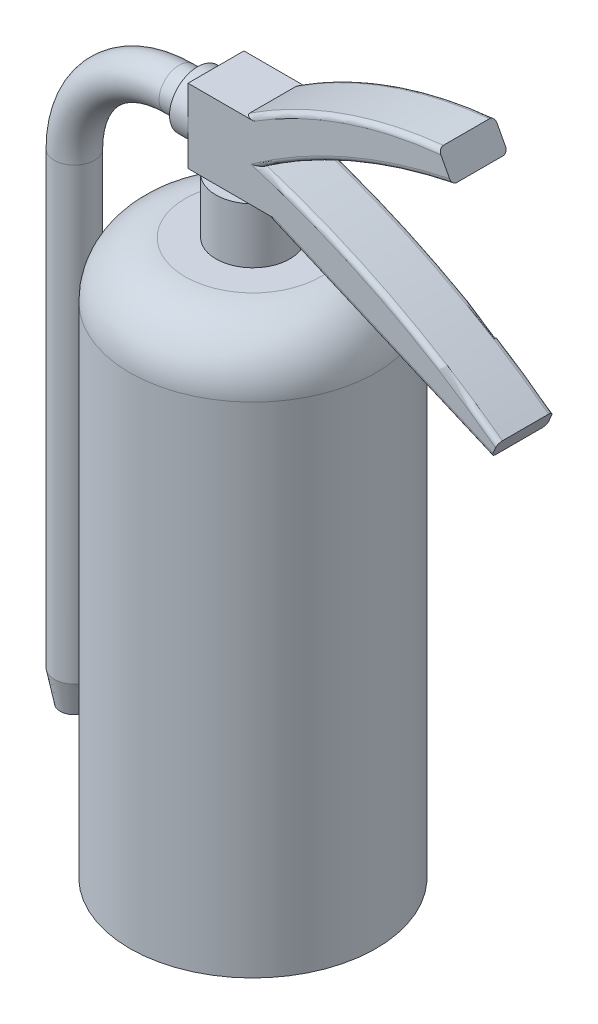
SolidWorks part; units mm, degrees
ref_plane "Alzado" through (0, 0, 0) normal (0, 0, 1) x (1, 0, 0)
ref_plane "Planta" through (0, 0, 0) normal (0, 1, 0) x (1, 0, 0)
ref_plane "Vista lateral" through (0, 0, 0) normal (1, 0, 0) x (0, 0, -1)
sketch "Croquis1" plane through (0, 0, 0) normal (0, 1, 0) x (1, 0, 0)
  circle A0 centre (0, 0) radius 200
  dimension "D1" = 400
extrude "Saliente-Extruir1" add sketch "Croquis1" along normal blind 900
fillet "Redondeo1" radius 90 1 edges at (0, 900, 200)
sketch "Croquis2" plane through (0, 900, 0) normal (0, 1, 0) x (1, 0, 0)
  circle A0 centre (0, 0) radius 60
  dimension "D1" = 120
extrude "Saliente-Extruir2" add sketch "Croquis2" along normal blind 90
sketch "Croquis3" plane through (0, 990, 0) normal (0, 1, 0) x (1, 0, 0)
  line L1 (60, -45.4181) -> (-60, -45.4181)
  line L2 (60, -45.4181) -> (60, 45.4181)
  line L3 (60, 45.4181) -> (-60, 45.4181)
  line L4 (-60, -45.4181) -> (-60, 45.4181)
  line L5 (60, -45.4181) -> (-60, 45.4181) construction
  line L6 (60, 45.4181) -> (-60, -45.4181) construction
  point P0 (0, 0)
extrude "Saliente-Extruir3" add sketch "Croquis3" along normal blind 60
sketch "Croquis4" plane through (0, 0, 45.4181) normal (0, 0, 1) x (1, 0, 0)
  line L0 (60, 990) -> (432.3041, 829.8986)
  line L1 (442.8785, 854.4887) -> (432.3041, 829.8986)
  line L2 (60, 1050) -> (60, 990)
  arc A0 (60, 1050) -> (442.8785, 854.4887) centre (-321.8825, -170.5176) cw
extrude "Saliente-Extruir4" add sketch "Croquis4" against normal up to surface (90.8363 mm away) up to face at (0, 1010, -45.4181)
sketch "Croquis5" plane through (0, 1050, 0) normal (0, 1, 0) x (1, 0, 0)
  line L1 (-60, 45.4181) -> (60, 45.4181)
  line L2 (-60, 45.4181) -> (-60, -45.4181)
  line L3 (-60, -45.4181) -> (60, -45.4181)
  line L4 (60, 45.4181) -> (60, -45.4181)
extrude "Saliente-Extruir5" add sketch "Croquis5" along normal blind 60
sketch "Croquis6" plane through (0, 0, 45.4181) normal (0, 0, 1) x (1, 0, 0)
  line L0 (-60, 1110) -> (60, 1110) construction
  line L1 (346.8148, 1222.0188) -> (368.8265, 1180.7468)
  line L2 (32.2307, 1110) -> (60, 1110)
  line L3 (60, 1110) -> (60, 1050)
  arc A0 (60, 1050) -> (368.8265, 1180.7468) centre (534.8675, 358.4545) cw
  arc A1 (32.2307, 1110) -> (346.8148, 1222.0188) centre (418.7121, 522.3735) cw
extrude "Saliente-Extruir6" add sketch "Croquis6" against normal up to surface (90.8363 mm away) up to face at (104.8285, 992.2879, -45.4181)
fillet "Redondeo2" radius 8 8 edges at (246.152, 909.9493, -45.4181) (246.152, 909.9493, 45.4181) (259.7136, 968.4483, -45.4181) (259.7136, 968.4483, 45.4181) (182.7782, 1184.9503, -45.4181) (182.7782, 1184.9503, 45.4181) (207.8131, 1130.9632, -45.4181) (207.8131, 1130.9632, 45.4181)
sketch "Croquis8" plane through (-60, 0, 0) normal (-1, 0, 0) x (0, 0, 1)
  circle A0 centre (0, 1050) radius 45.4181
extrude "Saliente-Extruir7" add sketch "Croquis8" along normal blind 30
sketch3d "Croquis3D1"
  line L0 (-90, 1050, 0) -> (-120, 1050, 0)
  line L1 (-90, 1050, 0) -> (-60, 1050, 0) construction
  line L2 (-290, 880, 0) -> (-290, 150, 0)
  arc A0 (-120, 1050, 0) -> (-290, 880, 0) centre (-120, 880, 0) ccw
  point P7 (-290, 1050, 0)
  point P8 (-120, 880, 170)
  dimension "D3" = 170
  dimension "D1" = 200
  dimension "D2" = 900
sketch "Croquis9" plane through (-90, 0, 0) normal (-1, 0, 0) x (0, 0, 1)
  circle A0 centre (0, 1050) radius 32.5
  dimension "D1" = 65
sweep "Barrer1" add profiles "Croquis9" path "Croquis3D1"
sketch "Croquis10" plane through (0, 150, 0) normal (0, -1, 0) x (1, 0, 0)
  circle A0 centre (-290, 0) radius 32.5
extrude "Saliente-Extruir8" add sketch "Croquis10" along normal blind 50 draft 11
